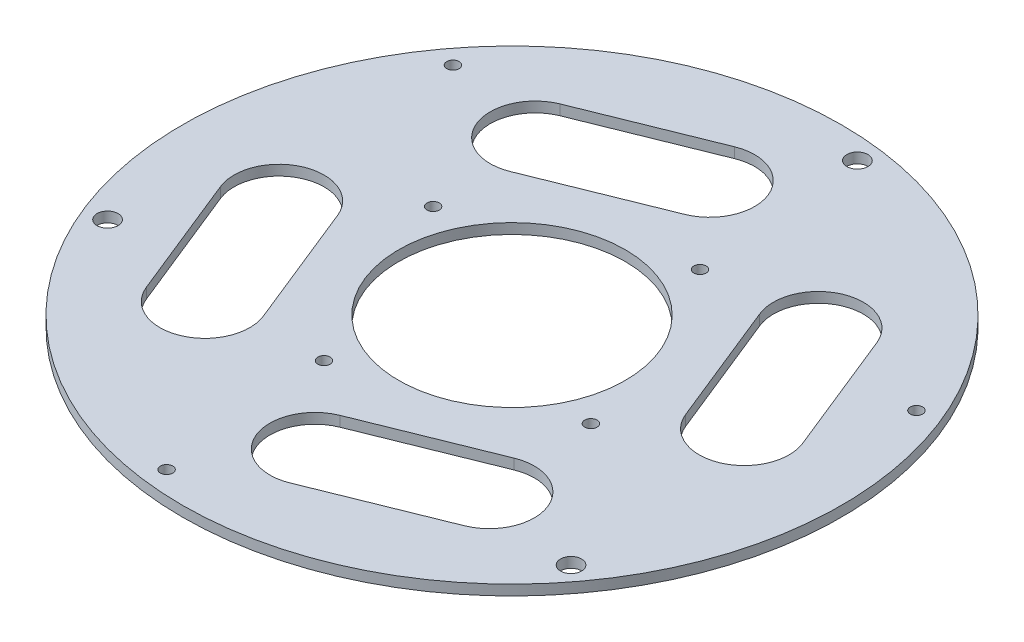
SolidWorks part; units mm, degrees
material "Aleación 1060"
ref_plane "Front Plane" through (0, 0, 0) normal (0, 0, 1) x (1, 0, 0)
ref_plane "Top Plane" through (0, 0, 0) normal (0, 1, 0) x (1, 0, 0)
ref_plane "Right Plane" through (0, 0, 0) normal (1, 0, 0) x (0, 0, -1)
sketch "Sketch1" plane through (0, 0, 0) normal (0, 1, 0) x (1, 0, 0)
  circle A0 centre (0, 0) radius 160
  circle A1 centre (0, 0) radius 55
  dimension "D1" = 0
extrude "Boss-Extrude1" add sketch "Sketch1" along normal blind 3
sketch "Sketch2" plane through (0, 3, 0) normal (0, 1, 0) x (1, 0, 0)
  circle A1 centre (0, 0) radius 70
  circle A2 centre (64.7949, -26.4882) radius 2.5
  dimension "D1" = 0
  dimension "D2" = 70
extrude "Cut-Extrude1" cut sketch "Sketch2" against normal blind 5 contours A2
pattern_circular "CirPattern1" count 4 over 360 about axis through (0, 0, 0) along (0, 1, 0) of "Cut-Extrude1"
sketch "Sketch3" plane through (0, 0, 0) normal (0, -1, 0) x (1, 0, 0)
  line L0 (64.7949, 26.4882) -> (26.4882, -64.7949)
  line L3 (45.6406, -19.1556) -> (138.3138, -58.0457)
  line L4 (138.3138, -58.0457) -> (64.7949, 26.4882)
  circle A0 centre (0, 0) radius 140
  circle A1 centre (138.3138, -58.0457) radius 5.1
  circle A2 centre (64.7949, 26.4882) radius 2.5 construction
  circle A6 centre (26.4882, -64.7949) radius 2.5 construction
  point P11 (45.6406, -19.1556)
  dimension "D1" = 0
  dimension "D2" = 10.2
  dimension "D4" = 0
  dimension "D14" = 150
  dimension "D3" = 0
  dimension "D5" = 0
  dimension "D6" = 0
  dimension "D7" = 0
  dimension "D8" = 49.495
  dimension "D9" = 0
  dimension "D10" = 0
  dimension "D11" = 0
  dimension "D12" = 90
  dimension "D13" = 0
extrude "Cut-Extrude3" cut sketch "Sketch3" against normal through all contours A0 A1 L4 L3 | L4 A1 L3
pattern_circular "CirPattern2" count 3 over 360 about axis through (0, 0, 0) along (0, 1, 0) of "Cut-Extrude3"
sketch "Sketch4" plane through (0, 3, 0) normal (0, 1, 0) x (1, 0, 0)
  line L0 (78.13, -76.3093) -> (-0.703, -108.0953) construction
  line L1 (87.4788, -99.4955) -> (8.6458, -131.2815)
  line L2 (68.7812, -53.1231) -> (-10.0519, -84.9091)
  arc A0 (87.4788, -99.4955) -> (68.7812, -53.1231) centre (78.13, -76.3093) ccw
  arc A1 (-10.0519, -84.9091) -> (8.6458, -131.2815) centre (-0.703, -108.0953) ccw
  point P2 (38.7135, -92.2023)
  dimension "D1" = 25
  dimension "D2" = 85
  dimension "D3" = 100
extrude "Cut-Extrude4" cut sketch "Sketch4" against normal through all
pattern_circular "CirPattern3" count 4 over 360 about axis through (0, 0, 0) along (0, 1, 0) of "Cut-Extrude4"
sketch "Sketch5" plane through (0, 3, 0) normal (0, 1, 0) x (1, 0, 0)
  circle A1 centre (0, 0) radius 160
extrude "Boss-Extrude2" add sketch "Sketch5" along normal blind 5 contours A1
sketch "Sketch6" plane through (0, 3, 0) normal (0, -1, 0) x (-1, 0, 0)
  circle A0 centre (-138.3138, 58.0457) radius 5.1
extrude "Cut-Extrude5" cut sketch "Sketch6" against normal blind 5
sketch "Sketch7" plane through (0, 3, 0) normal (0, -1, 0) x (-1, 0, 0)
  circle A0 centre (119.4259, 90.7604) radius 5.1
extrude "Cut-Extrude6" cut sketch "Sketch7" against normal blind 5
sketch "Sketch8" plane through (0, 3, 0) normal (0, -1, 0) x (-1, 0, 0)
  circle A0 centre (18.8878, -148.8061) radius 5.1
extrude "Cut-Extrude7" cut sketch "Sketch8" against normal blind 5
sketch "Sketch9" plane through (0, 3, 0) normal (0, -1, 0) x (-1, 0, 0)
  circle A0 centre (26.4882, -64.7949) radius 2.5
extrude "Cut-Extrude8" cut sketch "Sketch9" against normal blind 5
sketch "Sketch10" plane through (0, 3, 0) normal (0, -1, 0) x (-1, 0, 0)
  circle A0 centre (-64.7949, -26.4882) radius 2.5
extrude "Cut-Extrude9" cut sketch "Sketch10" against normal blind 5 contours A0
sketch "Sketch11" plane through (0, 3, 0) normal (0, -1, 0) x (-1, 0, 0)
  circle A0 centre (64.7949, 26.4882) radius 2.5
extrude "Cut-Extrude10" cut sketch "Sketch11" against normal blind 5 contours A0
sketch "Sketch12" plane through (0, 3, 0) normal (0, -1, 0) x (-1, 0, 0)
  circle A0 centre (-26.4882, 64.7949) radius 2.5
extrude "Cut-Extrude11" cut sketch "Sketch12" against normal blind 5
sketch "Sketch13" plane through (0, 3, 0) normal (0, -1, 0) x (-1, 0, 0)
  circle A1 centre (0, 0) radius 55
extrude "Cut-Extrude12" cut sketch "Sketch13" against normal blind 5
sketch "Sketch14" plane through (0, 3, 0) normal (0, -1, 0) x (-1, 0, 0)
  line L0 (16.7984, 124.7596) -> (77.0825, 100.4527)
  line L1 (-59.645, 60.6286) -> (-83.9519, 0.3445)
  line L4 (-100.1136, 77.0825) -> (-124.468, 16.6808)
  line L5 (84.291, -0.3445) -> (59.9367, -60.7462)
  line L6 (124.7596, -16.7984) -> (100.4527, -77.0825)
  line L7 (-115.3885, 48.0623) -> (-112.3145, 46.8228)
  line L8 (131.2815, -8.6458) -> (99.4955, -87.4788) construction
  line L9 (-69.0161, 29.3647) -> (-71.7985, 30.4865)
  line L10 (-53.1231, 68.7812) -> (-84.9091, -10.0519) construction
  line L11 (-131.2815, 8.6458) -> (-99.4955, 87.4788) construction
  line L12 (115.3885, -48.0623) -> (112.6062, -46.9404)
  line L13 (-48.0623, -115.3885) -> (-46.8228, -112.3145)
  line L14 (48.0623, 115.3885) -> (46.9404, 112.6062)
  line L15 (-29.3647, -69.0161) -> (-30.4865, -71.7985)
  line L16 (-77.0825, -100.1136) -> (-16.6808, -124.468)
  line L17 (-60.6286, -59.645) -> (-0.3445, -83.9519)
  line L18 (0.3445, 84.291) -> (60.7462, 59.9367)
  line L19 (48.0623, 115.3885) -> (46.9404, 112.6062)
  line L20 (8.6458, 131.2815) -> (87.4788, 99.4955) construction
  arc A1 (-124.468, 16.6808) -> (-83.9519, 0.3445) centre (-104.2099, 8.5126) ccw
  arc A3 (59.9367, -60.7462) -> (100.4527, -77.0825) centre (80.1947, -68.9143) ccw
  arc A5 (-59.645, 60.6286) -> (-100.161, 76.9649) centre (-79.8793, 68.8555) ccw
  arc A6 (124.7596, -16.7984) -> (84.2436, -0.4621) centre (104.5253, -8.5714) ccw
  arc A7 (-16.6808, -124.468) -> (-0.3445, -83.9519) centre (-8.5126, -104.2099) ccw
  arc A8 (-60.6286, -59.645) -> (-76.9649, -100.161) centre (-68.8555, -79.8793) ccw
  arc A9 (16.7984, 124.7596) -> (0.4621, 84.2436) centre (8.5714, 104.5253) ccw
  arc A10 (60.7462, 59.9367) -> (77.0825, 100.4527) centre (68.9143, 80.1947) ccw
extrude "Cut-Extrude15" cut sketch "Sketch14" against normal blind 5 contours L17 A8 L16 A7 | L6 A6 L5 A3 | L1 A5 L4 A1 | L18 A10 L0 A9
sketch "Sketch15" plane through (0, 0, 0) normal (0, -1, 0) x (1, 0, 0)
  circle A0 centre (0, 0) radius 160
extrude "Cut-Extrude16" cut sketch "Sketch15" against normal blind 3
sketch "Sketch16" plane through (0, 3, 0) normal (0, -1, 0) x (-1, 0, 0)
  line L3 (-65.9454, 16.8302) -> (-58.206, 35.272)
  line L4 (-58.206, 35.272) -> (-12.1014, 15.9235)
  line L5 (47.5481, 48.6953) -> (59.6495, 32.7718)
  line L6 (-65.9454, 16.8302) -> (-19.8408, -2.5184)
  line L7 (18.3973, -65.5255) -> (-1.4435, -68.0439)
  line L8 (18.3973, -65.5255) -> (12.1014, -15.9235)
  line L9 (-1.4435, -68.0439) -> (-7.7394, -18.4418)
  line L10 (47.5481, 48.6953) -> (7.7394, 18.4418)
  line L11 (59.6495, 32.7718) -> (19.8408, 2.5184)
  arc A0 (-19.8408, -2.5184) -> (-7.7394, -18.4418) centre (0, 0) ccw
  arc A1 (12.1014, -15.9235) -> (19.8408, 2.5184) centre (0, 0) ccw
  arc A2 (7.7394, 18.4418) -> (-12.1014, 15.9235) centre (0, 0) ccw
extrude "Boss-Extrude4" add sketch "Sketch16" along normal blind 14
sketch "Sketch20" plane through (0, 3, 0) normal (0, 1, 0) x (1, 0, 0)
  circle A0 centre (0, 0) radius 18
extrude "Cut-Extrude19" cut sketch "Sketch20" against normal blind 13
sketch "Sketch21" plane through (0, -11, 0) normal (0, -1, 0) x (1, 0, 0)
  line L1 (-48.1531, -47.8991) -> (-59.0444, -33.568)
  line L4 (1.4435, 68.0439) -> (-18.3973, 65.5255) construction
  line L9 (-48.1531, -47.8991) -> (1.3086, -10.3096)
  line L10 (-59.0444, -33.568) -> (-9.5827, 4.0215)
  line L11 (58.5929, -34.3499) -> (65.5584, -17.7523)
  line L12 (-17.4053, 65.6514) -> (0.4514, 67.9179)
  line L15 (8.2741, 6.2881) -> (65.5584, -17.7523)
  line L16 (8.2741, 6.2881) -> (0.4514, 67.9179)
  line L17 (1.3086, -10.3096) -> (58.5929, -34.3499)
  line L18 (-9.5827, 4.0215) -> (-17.4053, 65.6514)
extrude "Cut-Extrude21" cut sketch "Sketch21" against normal blind 14
sketch "Sketch22" plane through (0, -11, 0) normal (0, -1, 0) x (-1, 0, 0)
  line L0 (12.1014, -15.9235) -> (18.3973, -65.5255)
  line L1 (18.3973, -65.5255) -> (-1.4435, -68.0439)
  line L2 (-1.4435, -68.0439) -> (-7.6534, -19.1196)
  line L3 (-7.7394, -18.4418) -> (-1.4435, -68.0439) construction
  line L4 (-19.8408, -2.5184) -> (-65.9454, 16.8302)
  line L5 (-65.9454, 16.8302) -> (-58.206, 35.272)
  line L6 (-58.206, 35.272) -> (-12.1014, 15.9235)
  line L7 (7.7394, 18.4418) -> (47.5481, 48.6953)
  line L8 (47.5481, 48.6953) -> (7.7394, 18.4418) construction
  line L9 (47.5481, 48.6953) -> (37.0089, 40.6859) construction
  line L10 (47.5481, 48.6953) -> (59.6495, 32.7718)
  line L11 (59.6495, 32.7718) -> (19.8408, 2.5184)
  line L18 (-0.4514, -67.9179) -> (-8.2741, -6.2881)
  line L19 (-8.2741, -6.2881) -> (-65.5584, 17.7523)
  line L20 (-65.5584, 17.7523) -> (-65.9454, 16.8302)
  line L21 (-65.9454, 16.8302) -> (-19.8408, -2.5184)
  line L22 (-7.7394, -18.4418) -> (-1.4435, -68.0439)
  line L23 (-1.4435, -68.0439) -> (-0.4514, -67.9179)
  line L28 (-7.7394, -18.4418) -> (-7.6534, -19.1196)
  arc A0 (12.1014, -15.9235) -> (19.8408, 2.5184) centre (0, 0) ccw
  arc A1 (7.7394, 18.4418) -> (-12.1014, 15.9235) centre (0, 0) ccw
  arc A3 (-19.8408, -2.5184) -> (-7.7394, -18.4418) centre (0, 0) ccw
  arc A4 (-19.8408, -2.5184) -> (-7.7394, -18.4418) centre (0, 0) ccw
  dimension "D1" = 0
extrude "Cut-Extrude24" add sketch "Sketch22" along normal blind 14
sketch "Sketch23" plane through (0, 8, 0) normal (0, 1, 0) x (1, 0, 0)
  circle A0 centre (-119.4259, 90.7604) radius 5.1
  circle A1 centre (138.3138, 58.0457) radius 5.1
  circle A2 centre (-18.8878, -148.8061) radius 5.1
  circle A4 centre (-138.3138, -58.0457) radius 5.1
  circle A5 centre (18.8878, 148.8061) radius 5.1
  circle A6 centre (119.4259, -90.7604) radius 5.1
extrude "Cut-Extrude22" cut sketch "Sketch23" against normal blind 5
sketch "Sketch24" plane through (0, 8, 0) normal (0, 1, 0) x (1, 0, 0)
  circle A0 centre (64.7949, -26.4882) radius 3
  circle A1 centre (-26.4882, -64.7949) radius 3
  circle A2 centre (-64.7949, 26.4882) radius 3
  circle A3 centre (26.4882, 64.7949) radius 3
extrude "Cut-Extrude23" cut sketch "Sketch24" against normal blind 10 contours A1 | A0 | A3 | A2
sketch "Sketch25" plane through (0, 8, 0) normal (0, 1, 0) x (1, 0, 0)
  circle A0 centre (-119.4259, 90.7604) radius 3
  circle A1 centre (138.3138, 58.0457) radius 3
  circle A2 centre (-18.8878, -148.8061) radius 3
  circle A3 centre (-119.4259, 90.7604) radius 5.1
  circle A5 centre (138.3138, 58.0457) radius 5.1
  circle A6 centre (-18.8878, -148.8061) radius 5.1
extrude "Boss-Extrude6" add sketch "Sketch25" against normal blind 5
sketch "Sketch26" plane through (0, 3, 0) normal (0, -1, 0) x (-1, 0, 0)
  line L0 (64.9579, -16.4157) -> (57.2184, -34.8576)
  line L1 (-46.6954, -48.0473) -> (-58.7968, -32.1238)
  line L2 (1.5783, 66.9814) -> (-18.2625, 64.463)
  line L3 (-7.7394, -18.4418) -> (-46.6954, -48.0473)
  line L4 (1.5783, 66.9814) -> (7.7394, 18.4418)
  line L5 (57.2184, -34.8576) -> (12.1014, -15.9235)
  line L6 (64.9579, -16.4157) -> (19.8408, 2.5184)
  line L7 (-19.8408, -2.5184) -> (-58.7968, -32.1238)
  line L8 (-18.2625, 64.463) -> (-12.1014, 15.9235)
  line L9 (4.1767, 70.3353) -> (-21.6164, 67.0614)
  line L10 (-21.6164, 67.0614) -> (-15.2857, 17.1857)
  line L11 (-22.9722, -1.1301) -> (-63.0005, -31.5505)
  line L12 (-47.2687, -52.251) -> (-63.0005, -31.5505)
  line L13 (-7.2404, -21.8306) -> (-47.2687, -52.251)
  line L14 (58.8238, -38.7848) -> (12.4648, -19.3295)
  line L15 (68.885, -14.8104) -> (58.8238, -38.7848)
  line L16 (68.885, -14.8104) -> (22.5261, 4.6449)
  line L17 (4.1767, 70.3353) -> (10.5074, 20.4596)
  arc A0 (19.8408, 2.5184) -> (7.7394, 18.4418) centre (0, 0) ccw
  arc A1 (-7.7394, -18.4418) -> (12.1014, -15.9235) centre (0, 0) ccw
  arc A2 (-12.1014, 15.9235) -> (-19.8408, -2.5184) centre (0, 0) ccw
  arc A4 (-15.2857, 17.1857) -> (-22.9722, -1.1301) centre (0, 0) ccw
  arc A5 (-7.2404, -21.8306) -> (12.4648, -19.3295) centre (0, 0) ccw
  arc A6 (22.5261, 4.6449) -> (10.5074, 20.4596) centre (0, 0) ccw
  point P8 (6.0507, -7.9617)
  point P9 (-113.3752, -98.7221)
  point P10 (-8.9674, 150.0653)
  point P11 (9.9204, 1.2592)
  point P12 (134.4441, -67.2666)
  point P13 (-3.8697, -9.2209)
  point P14 (142.1835, -48.8248)
  point P15 (3.8697, 9.2209)
  point P16 (-6.0507, 7.9617)
  point P17 (-125.4766, -82.7987)
  point P18 (-28.8083, 147.5469)
  point P19 (-9.9204, -1.2592)
  dimension "D1" = 3
extrude "Boss-Extrude7" add sketch "Sketch26" along normal blind 12
sketch "Sketch27" plane through (0, -9, 0) normal (0, -1, 0) x (1, 0, 0)
  line L0 (-4.1767, -70.3353) -> (21.6164, -67.0614)
  line L1 (21.6164, -67.0614) -> (15.2857, -17.1857)
  line L2 (-10.5074, -20.4596) -> (-4.1767, -70.3353)
  line L3 (-22.5261, -4.6449) -> (-68.885, 14.8104)
  line L4 (-68.885, 14.8104) -> (-58.8238, 38.7848)
  line L5 (-58.8238, 38.7848) -> (-12.4648, 19.3295)
  line L6 (47.2687, 52.251) -> (7.2404, 21.8306)
  line L7 (47.2687, 52.251) -> (63.0005, 31.5505)
  line L8 (63.0005, 31.5505) -> (22.9722, 1.1301)
  arc A0 (-22.5261, -4.6449) -> (-10.5074, -20.4596) centre (0, 0) ccw
  arc A1 (7.2404, 21.8306) -> (-12.4648, 19.3295) centre (0, 0) ccw
  arc A2 (15.2857, -17.1857) -> (22.9722, 1.1301) centre (0, 0) ccw
extrude "Boss-Extrude8" add sketch "Sketch27" along normal blind 2
sketch "Sketch28" plane through (8.7198, 0, -68.6983) normal (0.1259, 0, -0.992) x (-0.992, 0, -0.1259)
  line L0 (-13, 3) -> (-13, -11)
  line L1 (-13, -11) -> (13, -11)
  line L2 (13, -11) -> (13, 3)
  line L3 (13, 3) -> (-13, 3)
  line L4 (11, 1) -> (-11, 1)
  line L5 (-11, 1) -> (-11, -9)
  line L6 (-11, -9) -> (11, -9)
  line L7 (11, -9) -> (11, 1)
  dimension "D1" = 2
extrude "Cut-Extrude25" cut sketch "Sketch28" against normal blind 15 contours L4 L5 L6 L7
sketch "Sketch29" plane through (-63.8544, 0, 26.7976) normal (-0.9221, 0, 0.387) x (0.387, 0, 0.9221)
  line L0 (-13, -11) -> (13, -11)
  line L2 (13, -11) -> (13, 3)
  line L3 (13, 3) -> (-13, 3)
  line L4 (-13, 3) -> (-13, -11)
  line L5 (-11, 1) -> (-11, -9)
  line L6 (-11, -9) -> (11, -9)
  line L7 (11, -9) -> (11, 1)
  line L8 (11, 1) -> (-11, 1)
  dimension "D1" = 2
extrude "Cut-Extrude26" cut sketch "Sketch29" against normal blind 15 contours L5 L6 L7 L8
sketch "Sketch30" plane through (55.1346, 0, 41.9008) normal (0.7962, 0, 0.6051) x (0.6051, 0, -0.7962)
  line L0 (-13, -11) -> (13, -11)
  line L1 (13, -11) -> (13, 3)
  line L2 (13, 3) -> (-13, 3)
  line L3 (-13, 3) -> (-13, -11)
  line L4 (-11, 1) -> (-11, -9)
  line L5 (-11, -9) -> (11, -9)
  line L6 (11, -9) -> (11, 1)
  line L7 (11, 1) -> (-11, 1)
  dimension "D1" = 2
extrude "Cut-Extrude27" cut sketch "Sketch30" against normal blind 15 contours L4 L5 L6 L7
sketch "Croquis1" plane through (0, 3, 0) normal (0, -1, 0) x (1, 0, 0)
  circle A0 centre (0, 0) radius 160
extrude "Cortar-Extruir1" cut sketch "Croquis1" along normal through all
sketch "Croquis2" plane through (0, 0, 0) normal (0, 1, 0) x (1, 0, 0)
  line L0 (-84.291, -0.3445) -> (-59.9367, -60.7462) construction
  line L1 (-60.7462, 59.9367) -> (-0.3445, 84.291)
  line L2 (-77.0825, 100.4527) -> (-16.7984, 124.7596)
  line L3 (-124.7596, -16.7984) -> (-112.6062, -46.9404)
  line L4 (-124.7596, -16.7984) -> (-100.4527, -77.0825) construction
  line L5 (-84.291, -0.3445) -> (-72.1138, -30.5453)
  line L6 (-112.6062, -46.9404) -> (0, 0) construction
  line L7 (0, 0) -> (-38.7429, 92.36) construction
  line L8 (-68.9143, 80.1947) -> (-8.5714, 104.5253) construction
  line L9 (-138.3138, -58.0457) -> (-112.6062, -46.9404) construction
  circle A0 centre (0, 0) radius 160
  arc A1 (-0.3445, 84.291) -> (-16.7984, 124.7596) centre (-8.5714, 104.5253) ccw
  arc A2 (-60.7462, 59.9367) -> (-77.0825, 100.4527) centre (-68.9143, 80.1947) cw
  arc A3 (-124.7596, -16.7984) -> (-84.291, -0.3445) centre (-104.5253, -8.5714) cw
  arc A4 (-84.291, -0.3445) -> (-124.7596, -16.7984) centre (-104.5253, -8.5714) ccw construction
  arc A5 (-100.4527, -77.0825) -> (-59.9367, -60.7462) centre (-80.1947, -68.9143) ccw
  arc A6 (59.645, 60.6286) -> (100.1136, 77.0825) centre (79.8793, 68.8555) cw
  arc A7 (83.9519, 0.3445) -> (124.468, 16.6808) centre (104.2099, 8.5126) ccw
  circle A12 centre (0, 0) radius 55
  dimension "D1" = 21.8428
  dimension "D2" = 320
  dimension "D3" = 100.1568
  dimension "D5" = 21.8428
  dimension "D4" = 43.6855
